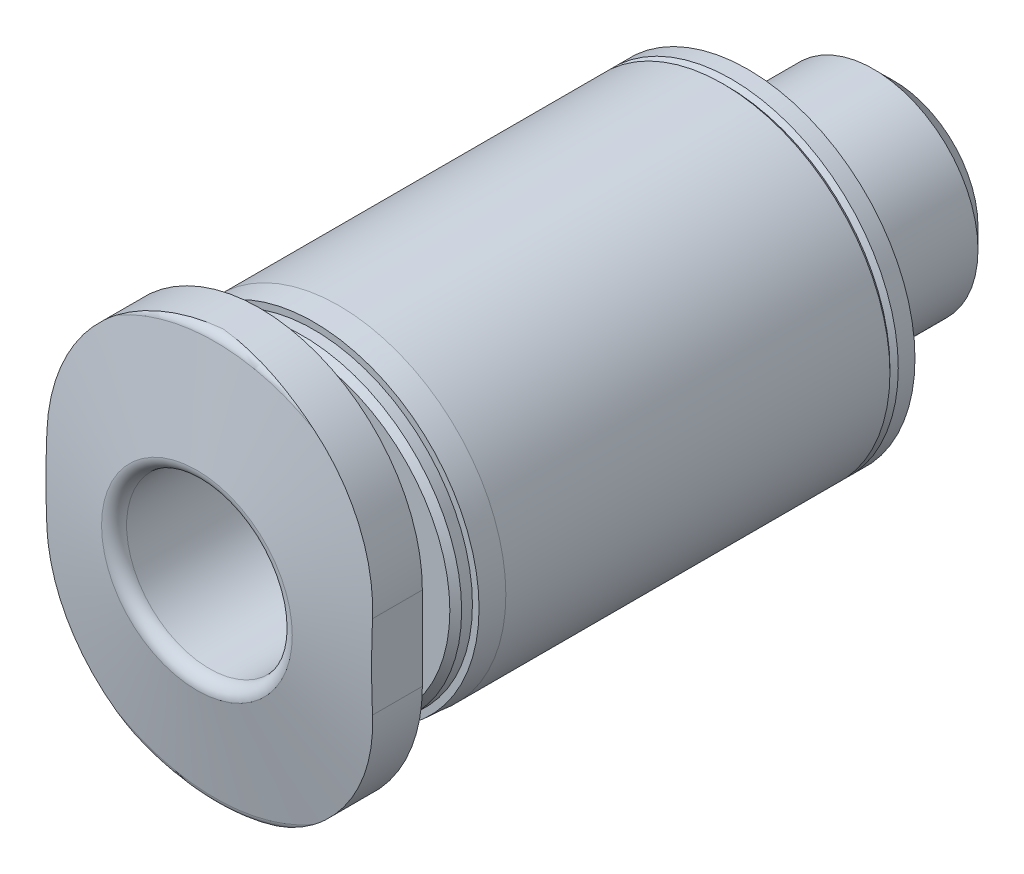
SolidWorks part; units mm, degrees
ref_plane "Front Plane" through (0, 0, 0) normal (0, 0, 1) x (1, 0, 0)
ref_plane "Top Plane" through (0, 0, 0) normal (0, 1, 0) x (1, 0, 0)
ref_plane "Right Plane" through (0, 0, 0) normal (1, 0, 0) x (0, 0, -1)
ref_plane "Plane1" through (0, 0, 0) normal (1, 0, 0) x (0, 0, -1)
sketch "Sketch1" plane through (0, 0, 0) normal (1, 0, 0) x (0, 0, -1)
  line L0 (-13.2, 0) -> (-13.2, 2.2845)
  line L1 (-13.2, 2.2845) -> (-12.768, 4.7347)
  line L2 (-12.571, 4.9) -> (-11.7, 4.9)
  line L3 (-11.7, 4.9) -> (-11.7, 3.0595)
  line L4 (-11.325, 2.6845) -> (-10.8, 2.6845)
  line L5 (-10.8, 2.6845) -> (-10.8, 3.6586)
  line L6 (-10.8, 3.6586) -> (-10.6586, 3.8)
  line L7 (-10.6586, 3.8) -> (-10.4, 3.8)
  line L8 (-10.4, 3.8) -> (-10.4, 3.958)
  line L9 (-10.4, 3.958) -> (-9.8, 4)
  line L10 (-9.8, 4) -> (-0.6, 4)
  line L11 (-0.6, 4) -> (-0.5, 3.9)
  line L12 (-0.5, 3.9) -> (-0.4, 4)
  line L13 (-0.4, 4) -> (0, 4)
  line L14 (0, 4) -> (0, 2.5)
  line L15 (0, 2.5) -> (3.0095, 2.5)
  line L16 (3.0095, 2.5) -> (3.5, 2.0095)
  line L17 (3.5, 2.0095) -> (3.5, 0)
  line L18 (3.5, 0) -> (-13.2, 0)
  line L19 (3.5, 0) -> (-13.2, 0) construction
  arc A0 (-12.768, 4.7347) -> (-12.571, 4.9) centre (-12.571, 4.7) cw
  arc A1 (-11.7, 3.0595) -> (-11.325, 2.6845) centre (-11.325, 3.0595) ccw
revolve "Revolve1" add sketch "Sketch1" angle 360 about L19
cosmetic thread "Cosmetic Thread1" parameters "D1"=3, "D2"=4.019
ref_plane "Plane2" through (0, 0, 13.2) normal (0, 0, 1) x (1, 0, 0)
sketch "Sketch2" plane through (0, 0, 13.2) normal (0, 0, 1) x (1, 0, 0)
  line L0 (-9.8, -9.8) -> (9.8, -9.8)
  line L1 (9.8, -9.8) -> (9.8, 9.8)
  line L2 (9.8, 9.8) -> (-9.8, 9.8)
  line L3 (-9.8, 9.8) -> (-9.8, -9.8)
  line L4 (-3.9, 1) -> (-3.9, -1)
  line L5 (3.9, -1) -> (3.9, 1)
  arc A0 (-3.9, -1) -> (3.9, -1) centre (0, -1) ccw
  arc A1 (3.9, 1) -> (-3.9, 1) centre (0, 1) ccw
extrude "Cut-Extrude1" cut sketch "Sketch2" against normal blind 1.5
ref_plane "Plane3" through (0, 0, -3.5) normal (0, 0, 1) x (1, 0, 0)
sketch "Sketch3" plane through (0, 0, -3.5) normal (0, 0, 1) x (1, 0, 0)
  line L0 (-1.25, -0.7217) -> (0, -1.4434)
  line L1 (0, -1.4434) -> (1.25, -0.7217)
  line L2 (1.25, -0.7217) -> (1.25, 0.7217)
  line L3 (1.25, 0.7217) -> (0, 1.4434)
  line L4 (0, 1.4434) -> (-1.25, 0.7217)
  line L5 (-1.25, 0.7217) -> (-1.25, -0.7217)
extrude "Cut-Extrude2" cut sketch "Sketch3" along normal blind 5.2
ref_plane "Plane4" through (0, 0, 0) normal (1, 0, 0) x (0, 0, -1)
sketch "Sketch4" plane through (0, 0, 0) normal (1, 0, 0) x (0, 0, -1)
  line L0 (-13.2, 0) -> (-13.2, 2.2845)
  line L1 (-12.9, 1.9845) -> (-1.7, 1.9845)
  line L2 (-1.7, 1.9845) -> (-1.7, 0)
  line L3 (-1.7, 0) -> (-13.2, 0)
  line L4 (-1.7, 0) -> (-13.2, 0) construction
  arc A0 (-13.2, 2.2845) -> (-12.9, 1.9845) centre (-12.9, 2.2845) ccw
revolve "Cut-Revolve1" cut sketch "Sketch4" angle 360 about L4
